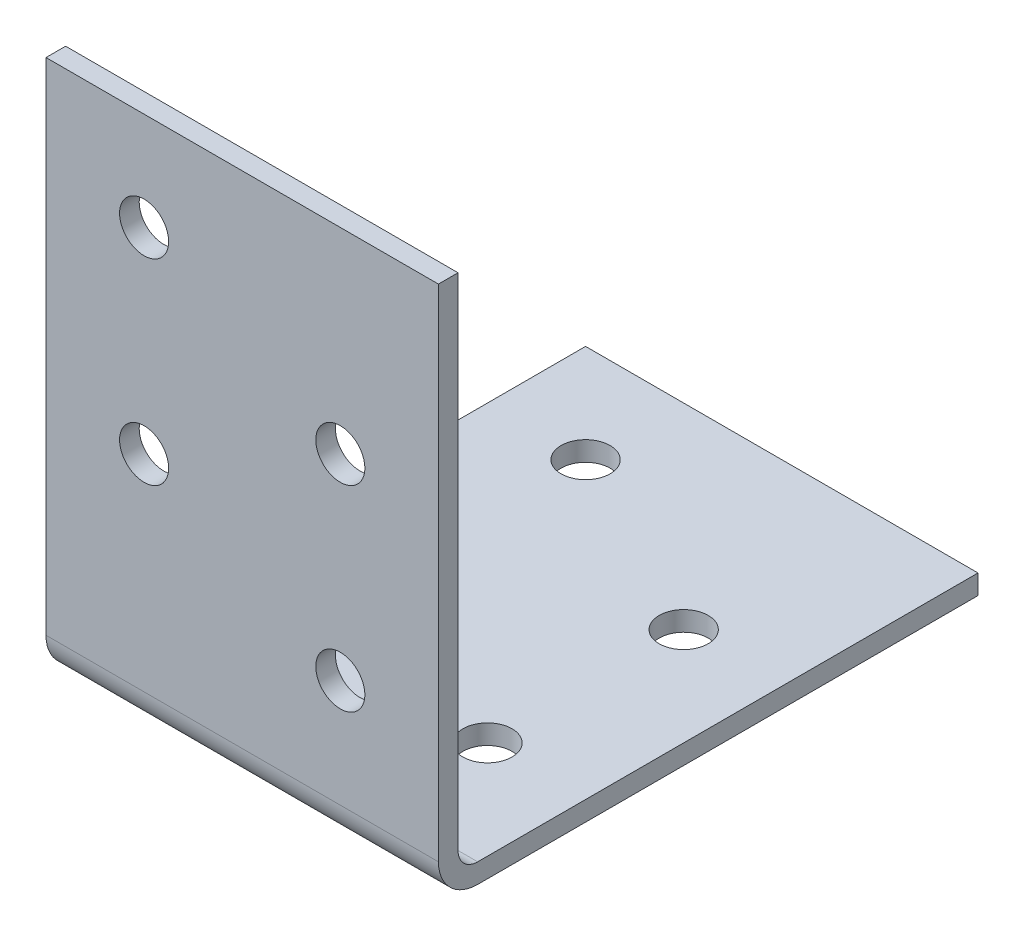
SolidWorks part; units mm, degrees
material "Acier non allié"
ref_plane "Plan de face" through (0, 0, 0) normal (0, 0, 1) x (1, 0, 0)
ref_plane "Plan de dessus" through (0, 0, 0) normal (0, 1, 0) x (1, 0, 0)
ref_plane "Plan de droite" through (0, 0, 0) normal (1, 0, 0) x (0, 0, -1)
sketch "Esquisse1" plane through (0, 0, 0) normal (1, 0, 0) x (0, 0, -1)
  line L0 (0, 55) -> (0, 4)
  line L1 (4, 0) -> (55, 0)
  line L2 (2, 55) -> (2, 4)
  line L3 (4, 2) -> (55, 2)
  line L4 (55, 2) -> (55, 0)
  line L5 (0, 55) -> (2, 55)
  arc A0 (0, 4) -> (4, 0) centre (4, 4) ccw
  arc A1 (2, 4) -> (4, 2) centre (4, 4) ccw
  point P6 (0, 0)
  dimension "D3" = 4
  dimension "D1" = 55
  dimension "D2" = 55
  dimension "D4" = 2
extrude "Boss.-Extru.1" add sketch "Esquisse1" along normal mid plane 40
hole_wizard "Diamètre du perçage Ø5.0 (5)1" positions "Esquisse3" profile "Esquisse2" hole size "Ø5.0" standard "ISO" end condition through all
sketch "Esquisse3" plane through (0, 2, 0) normal (0, 1, 0) x (1, 0, 0)
  line L0 (-10, 45) -> (-10, 25) construction
  line L1 (-10, 35) -> (10, 35) construction
  line L2 (10, 35) -> (10, 15) construction
  line L3 (20, 55) -> (-20, 55) construction
  line L4 (0, 35) -> (0, 55) construction
  point P0 (-10, 45)
  point P17 (-10, 25)
  point P20 (10, 35)
  point P23 (10, 15)
  dimension "D1" = 20
  dimension "D2" = 10
  dimension "D3" = 20
sketch "Esquisse2" plane through (-10, 2, -45) normal (1, 0, 0) x (0, 0, 1)
  line L0 (0, 0) -> (0, 2)
  line L1 (0, 2) -> (2.5, 2)
  line L2 (2.5, 2) -> (2.5, 0)
  line L5 (2.5, 0) -> (0, 0)
  line L11 (0, -6.35) -> (0, 107.95) construction
  dimension "Diamètre du perçage jusqu'au prochain" = 5
  dimension "Profondeur du perçage jusqu'au prochain" = 2
hole_wizard "Diamètre du perçage Ø5.0 (5)2" positions "Esquisse5" profile "Esquisse4" hole size "Ø5.0" standard "ISO" end condition through all
sketch "Esquisse5" plane through (0, 0, -2) normal (0, 0, -1) x (-1, 0, 0)
  line L0 (-10, 15) -> (-10, 35) construction
  line L1 (-10, 25) -> (10, 25) construction
  line L2 (10, 25) -> (10, 45) construction
  line L3 (0, 25) -> (0, 55) construction
  line L4 (-20, 55) -> (20, 55) construction
  point P0 (-10, 15)
  point P15 (-10, 35)
  point P18 (10, 25)
  point P21 (10, 45)
  dimension "D1" = 20
  dimension "D2" = 20
  dimension "D3" = 10
sketch "Esquisse4" plane through (10, 15, -2) normal (1, 0, 0) x (0, 1, 0)
  line L0 (0, 0) -> (0, 2)
  line L1 (0, 2) -> (2.5, 2)
  line L2 (2.5, 2) -> (2.5, 0)
  line L5 (2.5, 0) -> (0, 0)
  line L11 (0, -6.35) -> (0, 107.95) construction
  dimension "Diamètre du perçage jusqu'au prochain" = 5
  dimension "Profondeur du perçage jusqu'au prochain" = 2
